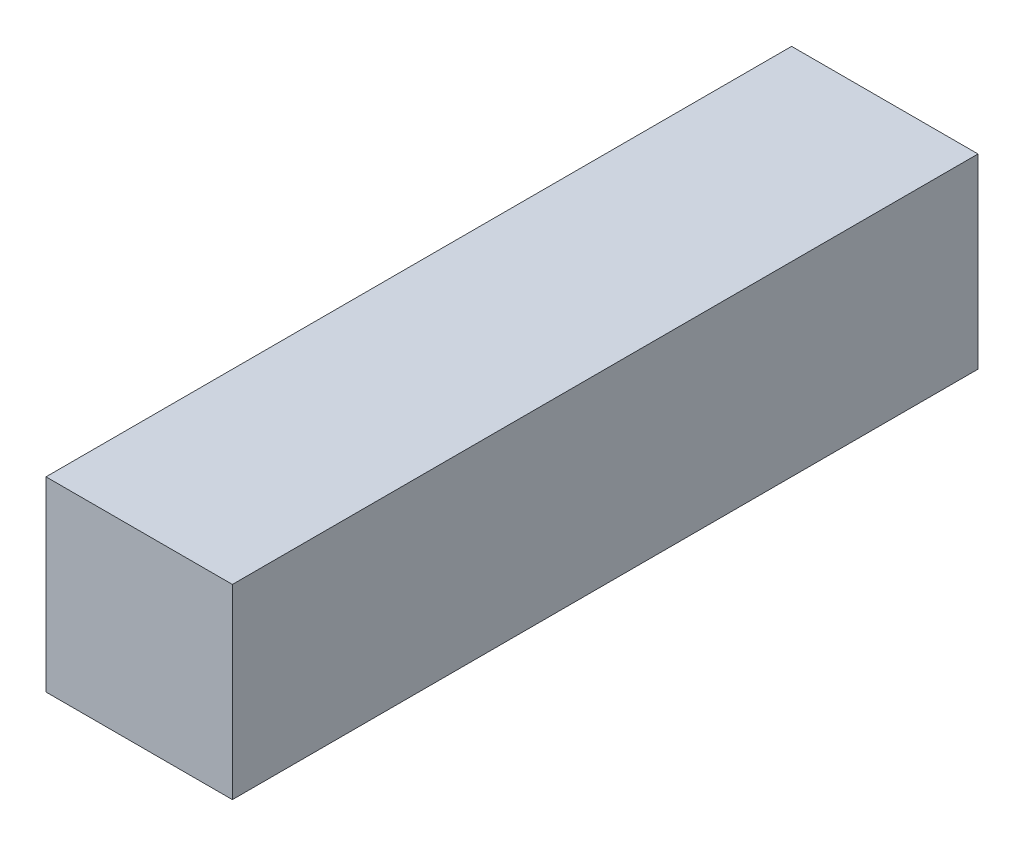
SolidWorks part; units mm, degrees
ref_plane "Front Plane" through (0, 0, 0) normal (0, 0, 1) x (1, 0, 0)
ref_plane "Top Plane" through (0, 0, 0) normal (0, 1, 0) x (1, 0, 0)
ref_plane "Right Plane" through (0, 0, 0) normal (1, 0, 0) x (0, 0, -1)
sketch "Sketch1" plane through (0, 0, 0) normal (1, 0, 0) x (0, 0, -1)
  line L0 (0, 0) -> (609.6, 0)
  line L1 (0, 0) -> (0, 152.4)
  line L2 (609.6, 0) -> (609.6, 152.4)
  line L3 (0, 152.4) -> (609.6, 152.4)
  dimension "D1" = 609.6
  dimension "D2" = 152.4
  dimension "D3" = 152.4
  dimension "D4" = 609.6
extrude "Boss-Extrude1" add sketch "Sketch1" along normal blind 152.4
